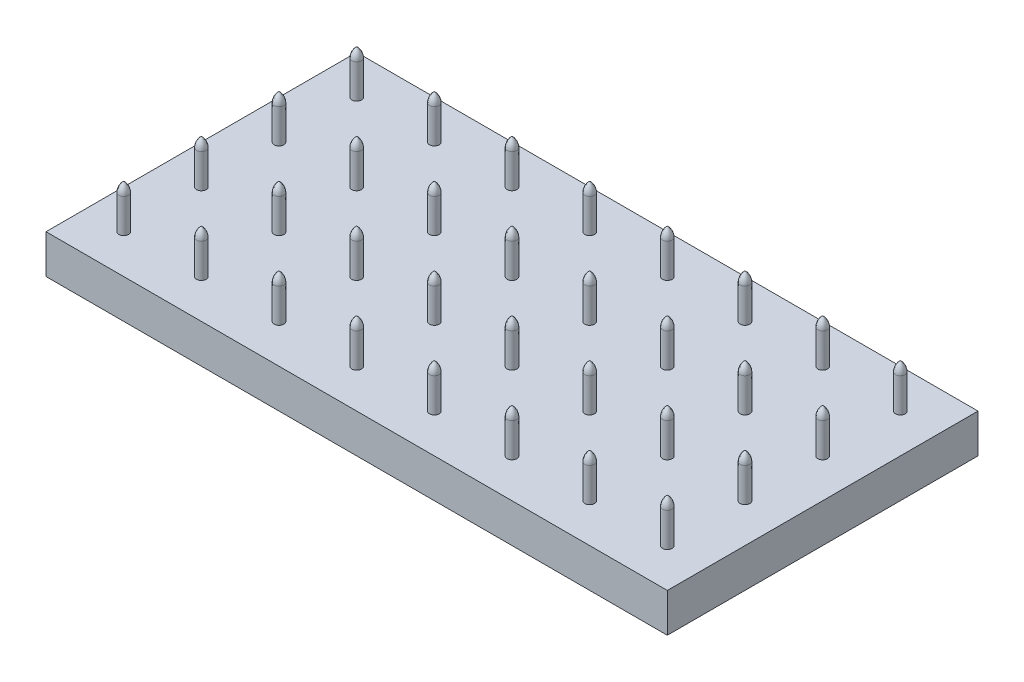
SolidWorks part; units mm, degrees
material "Silicon"
ref_plane "Front Plane" through (0, 0, 0) normal (0, 0, 1) x (1, 0, 0)
ref_plane "Top Plane" through (0, 0, 0) normal (0, 1, 0) x (1, 0, 0)
ref_plane "Right Plane" through (0, 0, 0) normal (1, 0, 0) x (0, 0, -1)
sketch "Sketch1" plane through (0, 0, 0) normal (0, 1, 0) x (1, 0, 0)
  line L1 (-50.8, -25.4) -> (50.8, -25.4)
  line L2 (-50.8, -25.4) -> (-50.8, 25.4)
  line L3 (-50.8, 25.4) -> (50.8, 25.4)
  line L4 (50.8, -25.4) -> (50.8, 25.4)
  line L5 (-50.8, -25.4) -> (50.8, 25.4) construction
  line L6 (-50.8, 25.4) -> (50.8, -25.4) construction
  point P0 (0, 0)
  dimension "D1" = 50.8
  dimension "D2" = 101.6
extrude "Boss-Extrude1" add sketch "Sketch1" along normal blind 6.35
sketch "Sketch3" plane through (0, 6.35, 0) normal (0, 1, 0) x (1, 0, 0)
  line L0 (-50.8, 25.4) -> (-44.45, 25.4) construction
  line L1 (50.8, 25.4) -> (-50.8, 25.4) construction
  line L2 (-44.45, 25.4) -> (-44.45, 19.05) construction
  line L3 (-44.45, 19.05) -> (-50.8, 19.05) construction
  line L4 (-50.8, 25.4) -> (-50.8, -25.4) construction
  line L5 (-50.8, 19.05) -> (-50.8, 25.4) construction
  dimension "D1" = 6.35
sketch "Sketch2" plane through (0, 6.35, 0) normal (0, 1, 0) x (1, 0, 0)
  line L0 (-44.45, 19.05) -> (-31.75, 19.05) construction
  circle A0 centre (-44.45, 19.05) radius 0.7937
  dimension "D3" = 12.7
extrude "Boss-Extrude2" add sketch "Sketch2" along normal blind 5.5563
ref_plane "Plane6" through (-44.45, 0, 0) normal (1, 0, 0) x (0, 0, -1)
sketch "Sketch12" plane through (-44.45, 0, 0) normal (1, 0, 0) x (0, 0, -1)
  line L0 (19.05, 6.35) -> (19.05, 11.9062) construction
  line L1 (19.05, 11.9062) -> (19.05, 13.4938)
  line L3 (19.05, 11.9062) -> (18.2563, 11.9062)
  arc A2 (19.05, 13.4938) -> (18.2563, 11.9062) centre (20.3259, 11.8636) ccw
revolve "Revolve1" add sketch "Sketch12" angle 360 about L0
pattern_linear "LPattern1" count 8 spacing 12.7 along (1, 0, 0) count 4 spacing 12.7 along (0, 0, 1) of "Boss-Extrude2", "Revolve1"
